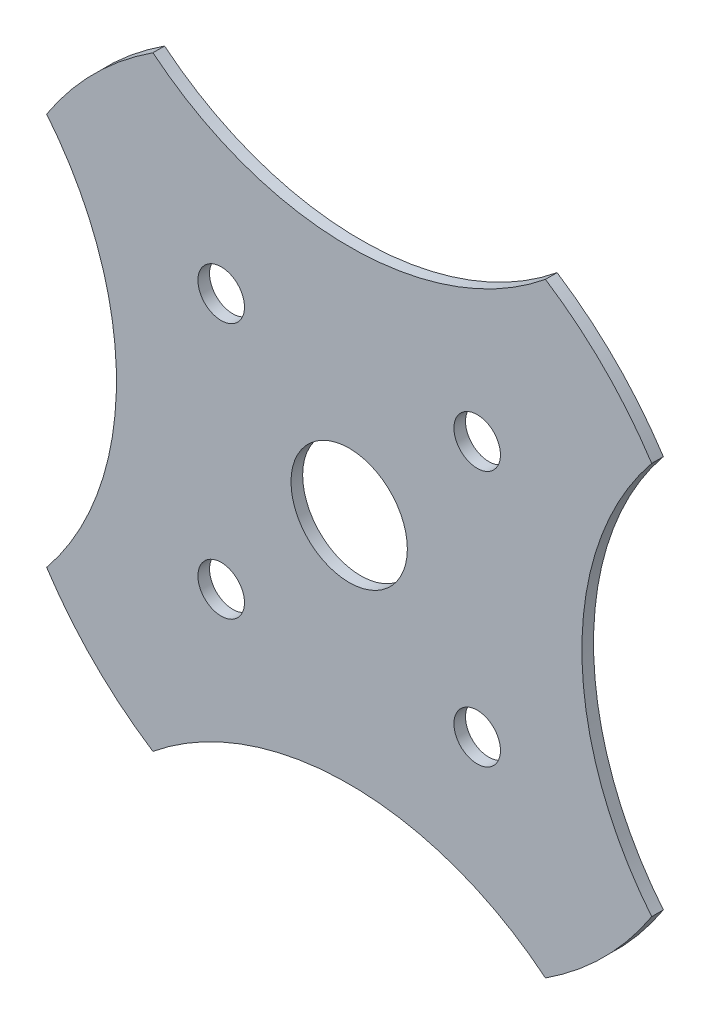
SolidWorks part; units mm, degrees
ref_plane "Front" through (0, 0, 0) normal (0, 0, 1) x (1, 0, 0)
ref_plane "Top" through (0, 0, 0) normal (0, 1, 0) x (1, 0, 0)
ref_plane "Right" through (0, 0, 0) normal (1, 0, 0) x (0, 0, -1)
sketch "Sketch1" plane through (0, 0, 0) normal (0, 0, 1) x (1, 0, 0)
  line L0 (-63.5, 0) -> (63.5, 0) construction
  line L1 (0, 63.5) -> (0, -63.5) construction
  arc A0 (-53.5535, 82.55) -> (53.5535, 82.55) centre (0, 148.3) ccw
  circle A1 centre (0, 0) radius 98.3996 construction
  arc A2 (-82.55, 53.5535) -> (-82.55, -53.5535) centre (-148.3, 0) cw
  arc A3 (-53.5535, -82.55) -> (53.5535, -82.55) centre (0, -148.3) cw
  arc A4 (82.55, 53.5535) -> (82.55, -53.5535) centre (148.3, 0) ccw
  arc A5 (-82.55, 53.5535) -> (-53.5535, 82.55) centre (0, 0) cw
  arc A6 (82.55, 53.5535) -> (53.5535, 82.55) centre (0, 0) ccw
  arc A7 (53.5535, -82.55) -> (82.55, -53.5535) centre (0, 0) ccw
  arc A8 (-82.55, -53.5535) -> (-53.5535, -82.55) centre (0, 0) ccw
  dimension "D1" = 127
  dimension "D2" = 165.1
extrude "Extrude1" add sketch "Sketch1" against normal blind 3.175
sketch "Sketch2" plane through (0, 0, -3.175) normal (0, 0, -1) x (-1, 0, 0)
  circle A0 centre (-34.925, 34.925) radius 6.35
  circle A1 centre (34.925, 34.925) radius 6.35
  circle A2 centre (34.925, -34.925) radius 6.35
  circle A3 centre (-34.925, -34.925) radius 6.35
  circle A4 centre (-34.925, -34.925) radius 4.7625 construction
  circle A5 centre (34.925, -34.925) radius 4.7625 construction
  circle A6 centre (34.925, 34.925) radius 4.7625 construction
  circle A7 centre (-34.925, 34.925) radius 4.7625 construction
  circle A8 centre (0, 0) radius 15.875
  dimension "D1" = 31.75
  dimension "D2" = 12.7
extrude "Cut-Extrude1" cut sketch "Sketch2" against normal up to next
